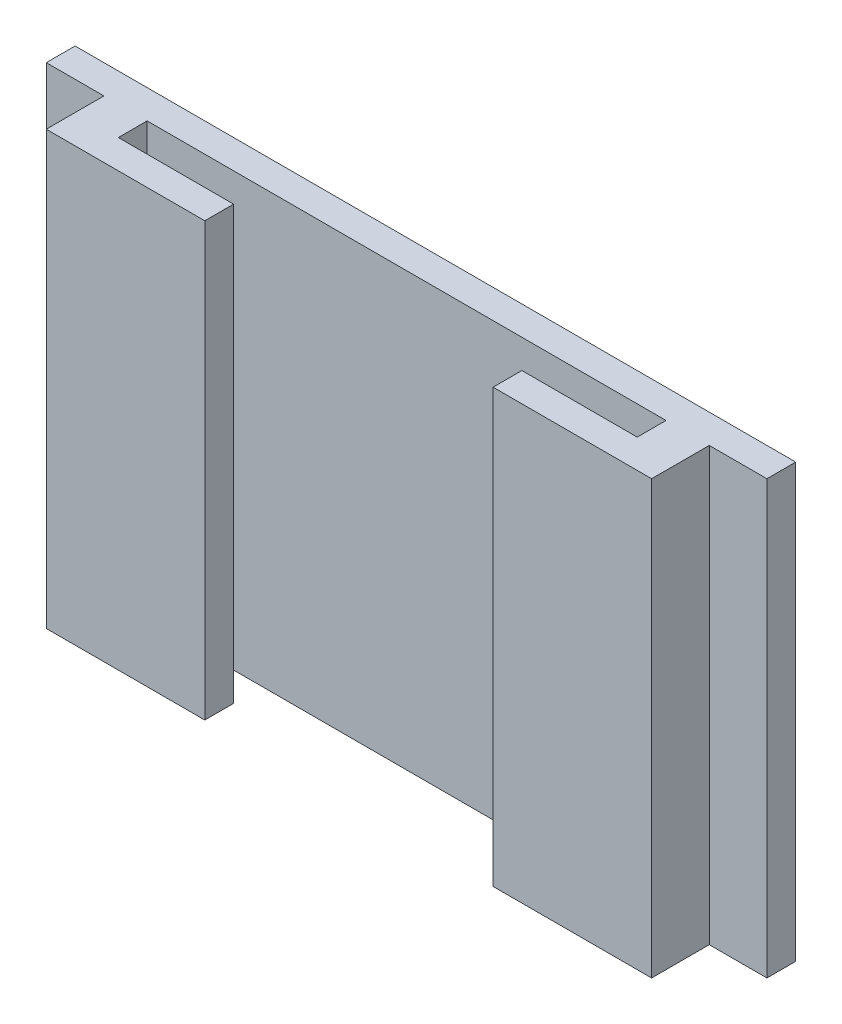
SolidWorks part; units mm, degrees
ref_plane "Front Plane" through (0, 0, 0) normal (0, 0, 1) x (1, 0, 0)
ref_plane "Top Plane" through (0, 0, 0) normal (0, 1, 0) x (1, 0, 0)
ref_plane "Right Plane" through (0, 0, 0) normal (1, 0, 0) x (0, 0, -1)
sketch "Sketch1" plane through (0, 0, 0) normal (0, 0, 1) x (1, 0, 0)
  line L1 (-12.5, 7.5) -> (12.5, 7.5)
  line L2 (-12.5, 7.5) -> (-12.5, -7.5)
  line L3 (-12.5, -7.5) -> (12.5, -7.5)
  line L4 (12.5, 7.5) -> (12.5, -7.5)
  line L5 (-12.5, 7.5) -> (12.5, -7.5) construction
  line L6 (-12.5, -7.5) -> (12.5, 7.5) construction
  point P0 (0, 0)
  dimension "D1" = 25
  dimension "D2" = 15
extrude "Boss-Extrude1" add sketch "Sketch1" along normal blind 1
sketch "Sketch2" plane through (0, 0, 0) normal (0, 0, 1) x (1, 0, 0)
  line L0 (-12.5, -7.5) -> (12.5, -7.5) construction
  line L1 (-10.5, 7.5) -> (10.5, 7.5)
  line L2 (-10.5, 7.5) -> (-10.5, -7.5)
  line L3 (-10.5, -7.5) -> (10.5, -7.5)
  line L4 (10.5, 7.5) -> (10.5, -7.5)
  line L5 (-10.5, 7.5) -> (10.5, -7.5) construction
  line L6 (-10.5, -7.5) -> (10.5, 7.5) construction
  point P0 (0, 0)
  dimension "D1" = 21
extrude "Boss-Extrude2" add sketch "Sketch2" along normal blind 3
sketch "Sketch3" plane through (0, 0, 0) normal (0, 1, 0) x (1, 0, 0)
  line L0 (10.5, -3) -> (-10.5, -3) construction
  line L1 (-9, -2) -> (-5, -2)
  line L2 (-9, -2) -> (-9, -1)
  line L3 (-9, -1) -> (9, -1)
  line L4 (9, -2) -> (9, -1)
  line L6 (-5, -2) -> (-5, -3)
  line L7 (-5, -3) -> (5, -3)
  line L8 (5, -2) -> (5, -3)
  line L9 (5, -2) -> (9, -2)
  dimension "D1" = 18
  dimension "D2" = 1
  dimension "D3" = 9
  dimension "D4" = 1
  dimension "D5" = 10
  dimension "D6" = 5
extrude "Cut-Extrude1" cut sketch "Sketch3" against normal through all both and the other way through all
